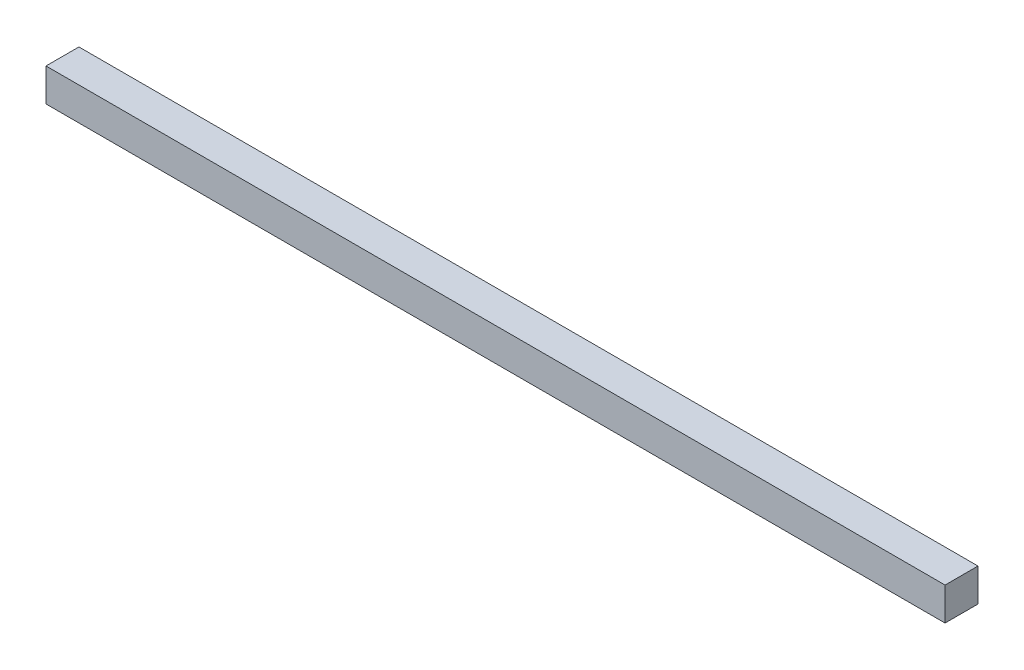
SolidWorks part; units mm, degrees
ref_plane "Plan de face" through (0, 0, 0) normal (0, 0, 1) x (1, 0, 0)
ref_plane "Plan de dessus" through (0, 0, 0) normal (0, 1, 0) x (1, 0, 0)
ref_plane "Plan de droite" through (0, 0, 0) normal (1, 0, 0) x (0, 0, -1)
sketch "Esquisse1" plane through (0, 0, 0) normal (0, 0, 1) x (1, 0, 0)
  line L1 (-87.5927, 45.5455) -> (185.4073, 45.5455)
  line L2 (-87.5927, 45.5455) -> (-87.5927, 35.5455)
  line L3 (-87.5927, 35.5455) -> (185.4073, 35.5455)
  line L4 (185.4073, 45.5455) -> (185.4073, 35.5455)
  dimension "D1" = 10
  dimension "D2" = 273
extrude "Boss.-Extru.1" add sketch "Esquisse1" along normal blind 10
equation "\"EpaisseurPlaque\"= 3"
equation "\"ProfondeurBoite\"=460"
equation "\"LongueurSyphon\"=270"
equation "\"LargeurSyphon\"=120"
equation "\"HauteurCoteDroit\"= 490"
equation "\"HauteurCoteGauche\"= 540"
equation "\"HauteurSolSyphon\"= 300"
equation "\"HauteurSyphon\"=\"HauteurCoteGauche\"-\"HauteurSolSyphon\""
equation "\"LargeurDroite\"=10"
equation "\"LargeurGauche\"=150"
equation "\"LargeurBoite\"= \"LargeurDroite\" + \"LargeurGauche\" + \"LargeurSyphon\""
equation "\"D2@Esquisse1\"=\"LongueurSyphon\" + 3"
